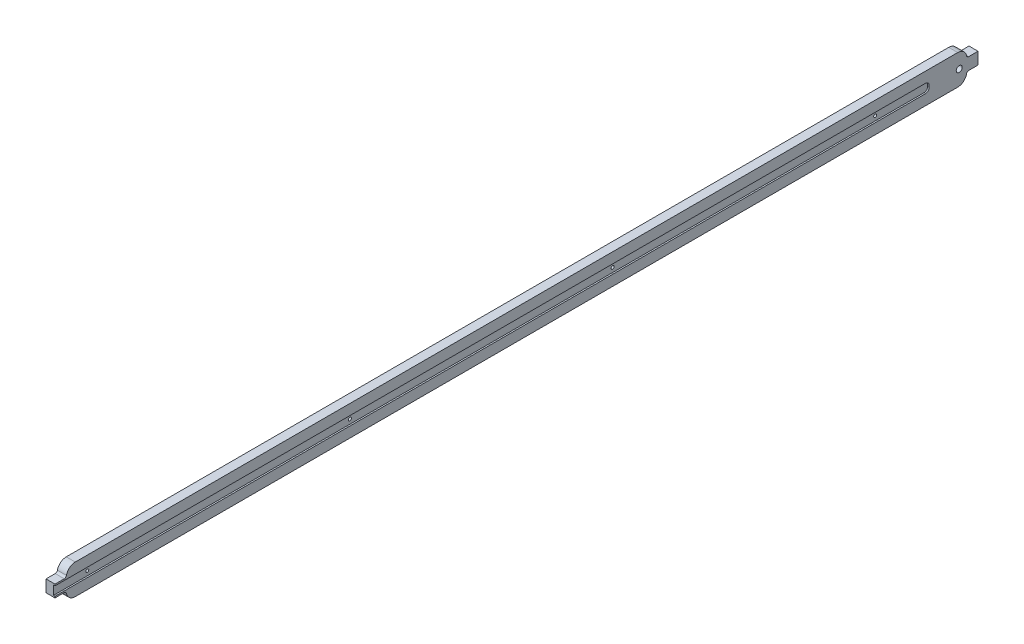
SolidWorks part; units mm, degrees
material "Pine"
ref_plane "Front Plane" through (0, 0, 0) normal (0, 0, 1) x (1, 0, 0)
ref_plane "Top Plane" through (0, 0, 0) normal (0, 1, 0) x (1, 0, 0)
ref_plane "Right Plane" through (0, 0, 0) normal (1, 0, 0) x (0, 0, -1)
sketch "Sketch1" plane through (0, 0, 0) normal (0, 0, 1) x (1, 0, 0)
  line L1 (-6, 20) -> (6, 20)
  line L2 (-6, 20) -> (-6, -20)
  line L3 (-6, -20) -> (6, -20)
  line L4 (6, 20) -> (6, -20)
  line L5 (-6, 20) -> (6, -20) construction
  line L6 (-6, -20) -> (6, 20) construction
  point P0 (0, 0)
  dimension "D1" = 12
  dimension "D2" = 40
extrude "Boss-Extrude1" add sketch "Sketch1" along normal mid plane 1200
fillet "Fillet1" radius 12 4 edges at (0, 20, 600) (0, -20, 600) (0, 20, -600) (0, -20, -600)
sketch "Sketch2" plane through (6, 0, 0) normal (1, 0, 0) x (0, 0, -1)
  line L0 (-600, -8) -> (-600, 8) construction
  line L1 (550, -6) -> (-600, -6)
  line L2 (550, -6) -> (550, 6)
  line L3 (550, 6) -> (-600, 6)
  line L4 (-600, -6) -> (-600, 6)
  line L5 (550, -6) -> (-600, 6) construction
  line L6 (550, 6) -> (-600, -6) construction
  line L7 (550, 0) -> (600, 0) construction
  line L8 (600, -8) -> (600, 8) construction
  point P0 (-25, 0)
  dimension "D1" = 12
  dimension "D2" = 50
extrude "Cut-Extrude1" cut sketch "Sketch2" against normal blind 2
fillet "Fillet2" radius 5 2 edges at (5, -6, -550) (5, 6, -550)
sketch "Sketch3" plane through (6, 0, 0) normal (1, 0, 0) x (0, 0, -1)
  line L0 (600, -8) -> (600, 8) construction
  line L1 (590, 0) -> (600, 0) construction
  circle A0 centre (590, 0) radius 4
  dimension "D1" = 8
  dimension "D2" = 10
extrude "Cut-Extrude2" cut sketch "Sketch3" against normal up to next
hole_wizard "Ø4.0 (4) Diameter Hole1" positions "Sketch5" profile "Sketch4" hole size "Ø4.0" standard "ISO" end condition up to next
sketch "Sketch5" plane through (-6, 0, 0) normal (-1, 0, 0) x (0, 0, 1)
  line L0 (600, 8) -> (600, -8) construction
  point P0 (570, 0)
  dimension "D1" = 30
sketch "Sketch4" plane through (-6, 0, 570) normal (0, 1, 0) x (0, 0, 1)
  line L0 (0, 0) -> (0, 10)
  line L1 (0, 10) -> (2, 10)
  line L2 (2, 10) -> (2, 0)
  line L5 (2, 0) -> (0, 0)
  line L11 (0, -6.35) -> (0, 107.95) construction
  dimension "Thru Hole Dia." = 4
  dimension "Thru Hole Depth" = 10
pattern_linear "LPattern1" count 4 spacing 350 along (0, 0, -1) of "Ø4.0 (4) Diameter Hole1"
sketch "Sketch6" plane through (-6, 0, 0) normal (-1, 0, 0) x (0, 0, 1)
  line L0 (-600, 8) -> (-615, 8)
  line L1 (-615, 8) -> (-615, -8)
  line L2 (-615, -8) -> (-600, -8)
  line L3 (600, 8) -> (615, 8)
  line L4 (615, 8) -> (615, -8)
  line L5 (615, -8) -> (600, -8)
  line L6 (600, 8) -> (600, -8) construction
  line L7 (600, 8) -> (600, -8)
  line L8 (-600, 8) -> (-600, -8) construction
  line L9 (-600, 8) -> (-600, -8)
  dimension "D1" = 15
  dimension "D2" = 15
extrude "Boss-Extrude2" add sketch "Sketch6" against normal blind 12
sketch "Sketch7" plane through (0, 0, 600) normal (0, 0, -1) x (-1, 0, 0)
  line L4 (-4, 6) -> (-6, 6)
  line L5 (-6, 6) -> (-6, -6)
  line L6 (-6, -6) -> (-4, -6)
  line L7 (-4, -6) -> (-4, 6)
  line L8 (-4, 6) -> (-6, 6)
  line L9 (-6, 6) -> (-6, -6)
  line L10 (-6, -6) -> (-4, -6)
  line L11 (-4, -6) -> (-4, 6)
  dimension "D1" = 0
extrude "Cut-Extrude6" cut sketch "Sketch7" against normal up to next
fillet "Fillet3" radius 3 4 edges at (0, -8, 600) (0, 8, 600) (0, -8, -600) (0, 8, -600)
